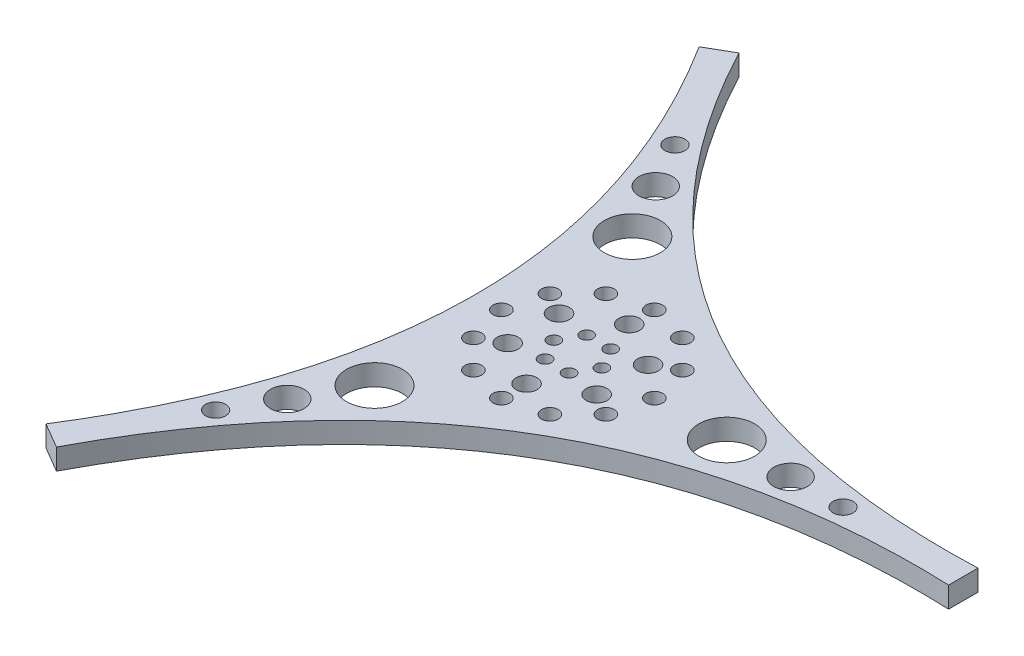
SolidWorks part; units mm, degrees
ref_plane "Спереди" through (0, 0, 0) normal (0, 0, 1) x (1, 0, 0)
ref_plane "Сверху" through (0, 0, 0) normal (0, 1, 0) x (1, 0, 0)
ref_plane "Справа" through (0, 0, 0) normal (1, 0, 0) x (0, 0, -1)
other "Configuration Table"
sketch "Эскиз1" plane through (0, 0, 0) normal (0, 1, 0) x (1, 0, 0)
  line L0 (49.0748, 85) -> (70.3158, 97.2842) construction
  line L5 (0, 0) -> (0, 170)
  line L6 (0, 0) -> (147.2243, 85)
  line L7 (0, 170) -> (147.2243, 85)
  line L8 (0, 163.0363) -> (6.0307, 166.5182)
  line L9 (141.1461, 81.4907) -> (141.1461, 88.5093)
  line L10 (0, 7.0293) -> (6.0307, 3.4818)
  line L11 (147.2243, 85) -> (0, 85) construction
  line L12 (0, 0) -> (73.6122, 127.5) construction
  line L13 (6.0307, 3.4818) -> (49.0748, 85) construction
  line L14 (49.0748, 85) -> (141.1461, 81.4907) construction
  line L15 (6.0307, 166.5182) -> (49.0748, 85) construction
  line L16 (49.0748, 85) -> (141.1461, 88.5093) construction
  line L17 (0, 163.0363) -> (49.0748, 85) construction
  line L18 (49.0748, 85) -> (0, 7.0293) construction
  line L19 (49.0748, 85) -> (51.9415, 80.0346) construction
  line L20 (49.0748, 85) -> (46.208, 80.0346) construction
  circle A3 centre (17.4031, 139.8569) radius 2.3925
  circle A4 centre (23.6655, 129.0102) radius 4.0079
  circle A5 centre (31.2927, 115.7995) radius 6.6785
  circle A6 centre (112.4181, 85) radius 2.3925
  circle A7 centre (99.8933, 85) radius 4.0079
  circle A8 centre (84.639, 85) radius 6.6785
  circle A9 centre (17.4031, 30.1431) radius 2.3925
  circle A10 centre (23.6655, 40.9898) radius 4.0079
  circle A11 centre (31.2927, 54.2005) radius 6.6785
  circle A15 centre (51.9415, 80.0346) radius 1.5
  circle A17 centre (46.208, 80.0346) radius 1.5
  circle A19 centre (43.3412, 85) radius 1.5
  circle A21 centre (46.208, 89.9654) radius 1.5
  circle A23 centre (51.9415, 89.9654) radius 1.5
  circle A25 centre (54.8083, 85) radius 1.5
  circle A27 centre (59.6953, 91.1421) radius 2.5
  circle A28 centre (59.7043, 78.8734) radius 2.5
  circle A29 centre (49.0837, 72.7313) radius 2.5
  circle A30 centre (38.4543, 78.8579) radius 2.5
  circle A31 centre (38.4453, 91.1266) radius 2.5
  circle A32 centre (49.0658, 97.2687) radius 2.5
  circle A39 centre (58.2067, 100.8169) radius 2
  circle A40 centre (64.8917, 94.1319) radius 2
  circle A41 centre (67.3386, 85) radius 2
  circle A42 centre (64.8917, 75.8681) radius 2
  circle A43 centre (58.2067, 69.1831) radius 2
  circle A44 centre (49.0748, 66.7362) radius 2
  circle A45 centre (39.9429, 69.1831) radius 2
  circle A46 centre (33.2579, 75.8681) radius 2
  circle A47 centre (30.811, 85) radius 2
  circle A48 centre (33.2579, 94.1319) radius 2
  circle A49 centre (39.9429, 100.8169) radius 2
  circle A50 centre (49.0748, 103.2638) radius 2
  spline S0 degree 1 poles (0, 0) (147.2243, 85) knots 0 0 1 1
  spline S1 degree 2 poles (0, 0) (73.6122, 42.5) (147.2243, 85) knots 0 0 0 1 1 1
  spline S2 degree 1 poles (6.0307, 3.4818) (141.1461, 81.4907) knots 0 0 1 1
  spline S3 degree 1 poles (6.0307, 166.5182) (141.1461, 88.5093) knots 0 0 1 1
  spline S4 degree 2 poles (6.0307, 3.4818) (49.0748, 85) (141.1461, 81.4907) knots 0 0 0 1 1 1
  spline S5 degree 2 poles (6.0307, 166.5182) (49.0748, 85) (141.1461, 88.5093) knots 0 0 0 1 1 1
  spline S6 degree 1 poles (0, 163.0363) (0, 7.0293) knots 0 0 1 1
  spline S7 degree 1 poles (0, 163.0363) (0, 7.0293) knots 0 0 1 1
  spline S8 degree 1 poles (0, 7.0293) (0, 163.0363) knots 0 0 1 1
  spline S9 degree 1 poles (0, 7.0293) (0, 163.0363) knots 0 0 1 1
  spline S10 degree 2 poles (0, 163.0363) (49.0748, 85) (0, 7.0293) knots 0 0 0 1 1 1
  point P6 (0, 0)
  point P20 (49.0748, 85)
  point P40 (49.0748, 85)
  point P70 (49.0748, 85)
  point P83 (49.0748, 85)
  point P95 (49.0748, 85)
  dimension "D2" = 3
  dimension "D3" = 6
  dimension "D4" = 6
  dimension "D5" = 12
  dimension "D1" = 2
extrude "Бобышка-Вытянуть4" add sketch "Эскиз1" along normal blind 5
